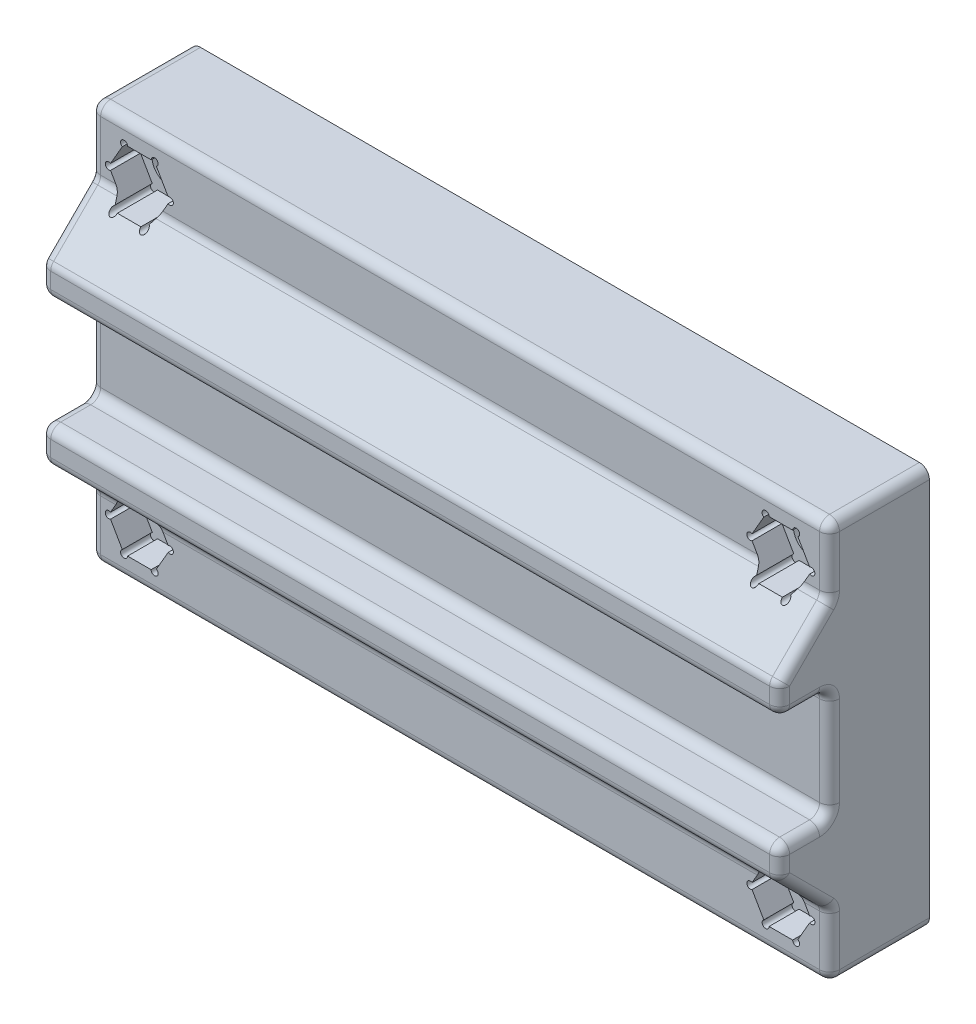
SolidWorks part; units mm, degrees
ref_plane "Front Plane" through (0, 0, 0) normal (0, 0, 1) x (1, 0, 0)
ref_plane "Top Plane" through (0, 0, 0) normal (0, 1, 0) x (1, 0, 0)
ref_plane "Right Plane" through (0, 0, 0) normal (1, 0, 0) x (0, 0, -1)
sketch "Sketch1" plane through (0, 0, 0) normal (0, 0, 1) x (1, 0, 0)
  line L7 (-37, -20) -> (37, -20)
  line L8 (-37, -20) -> (-37, 20)
  line L14 (-37, 20) -> (37, 20)
  line L15 (37, -20) -> (37, 20)
  line L18 (-37, -20) -> (37, 20) construction
  line L19 (-37, 20) -> (37, -20) construction
  point P0 (0, 0)
  dimension "D1" = 40
  dimension "D2" = 74
extrude "Boss-Extrude1" add sketch "Sketch1" along normal blind 10
sketch "Sketch2" plane through (-37, 0, 0) normal (-1, 0, 0) x (0, 0, 1)
  line L0 (10, 5.5) -> (15, 5.5)
  line L2 (15, 5.5) -> (15, 8.5)
  line L3 (15, 8.5) -> (10, 13.5)
  line L6 (10, 13.5) -> (10, 5.5)
  line L13 (0, 20) -> (0, -20)
  line L17 (0, -20) -> (10, -20)
  line L19 (10, -20) -> (10, 20)
  line L20 (10, 20) -> (0, 20)
  line L22 (0, 20) -> (0, -20) construction
  line L24 (0, -20) -> (10, -20) construction
  line L25 (10, -20) -> (10, 20) construction
  line L34 (10, 20) -> (0, 20) construction
  line L35 (0, 0) -> (10, 0) construction
  line L36 (10, -13.5) -> (10, -5.5)
  line L37 (15, -8.5) -> (10, -13.5)
  line L41 (15, -5.5) -> (15, -8.5)
  line L43 (10, -5.5) -> (15, -5.5)
  point P8 (10, 0)
  dimension "D2" = 3
  dimension "D3" = 5
  dimension "D4" = 5.5
  dimension "D5" = 45
  dimension "D1" = 0
extrude "Boss-Extrude2" add sketch "Sketch2" against normal up to surface (74 mm away) up to face at (37, 0, 5)
sketch "Sketch3" plane through (0, 0, 10) normal (0, 0, 1) x (1, 0, 0)
  line L0 (37, 20) -> (30.5, 13.5) construction
  line L1 (37, 13.5) -> (-37, 13.5) construction
  line L2 (37, 13.5) -> (37, 20) construction
  line L3 (33.75, 16.75) -> (30.5, 13.5) construction
  line L4 (8.25, 0) -> (-8.25, 0) construction
  line L5 (0, -8.25) -> (0, 8.25) construction
  circle A0 centre (32.125, 15.125) radius 1.75
  circle A1 centre (32.125, -15.125) radius 1.75
  circle A2 centre (-32.125, -15.125) radius 1.75
  circle A3 centre (-32.125, 15.125) radius 1.75
  point P22 (33.75, 16.75)
  dimension "D2" = 3.5
  dimension "D1" = 45
extrude "Cut-Extrude1" cut sketch "Sketch3" against normal through all both and the other way through all
sketch "Sketch4" plane through (0, 0, 10) normal (0, 0, 1) x (1, 0, 0)
  line L0 (30.595, 17.775) -> (30.42, 17.4719) construction
  line L7 (35.01, 15.4281) -> (33.83, 17.4719)
  line L8 (33.305, 17.775) -> (30.945, 17.775)
  line L9 (30.42, 17.4719) -> (29.24, 15.4281)
  line L10 (29.24, 14.8219) -> (30.42, 12.7781)
  line L11 (30.945, 12.475) -> (33.305, 12.475)
  line L12 (33.83, 12.7781) -> (35.01, 14.8219)
  line L13 (30.945, 17.775) -> (30.595, 17.775) construction
  line L14 (33.655, 17.775) -> (33.305, 17.775) construction
  line L15 (33.83, 17.4719) -> (33.655, 17.775) construction
  line L16 (35.185, 15.125) -> (35.01, 15.4281) construction
  line L17 (35.01, 14.8219) -> (35.185, 15.125) construction
  line L18 (33.655, 12.475) -> (33.83, 12.7781) construction
  line L19 (33.305, 12.475) -> (33.655, 12.475) construction
  line L20 (30.595, 12.475) -> (30.945, 12.475) construction
  line L21 (30.42, 12.7781) -> (30.595, 12.475) construction
  line L22 (29.065, 15.125) -> (29.24, 14.8219) construction
  line L23 (29.24, 15.4281) -> (29.065, 15.125) construction
  line L24 (-33.655, 17.775) -> (-33.83, 17.4719) construction
  line L25 (-29.24, 15.4281) -> (-30.42, 17.4719)
  line L26 (-30.945, 17.775) -> (-33.305, 17.775)
  line L27 (-33.83, 17.4719) -> (-35.01, 15.4281)
  line L28 (-35.01, 14.8219) -> (-33.83, 12.7781)
  line L29 (-33.305, 12.475) -> (-30.945, 12.475)
  line L30 (-30.42, 12.7781) -> (-29.24, 14.8219)
  line L31 (-33.305, 17.775) -> (-33.655, 17.775) construction
  line L32 (-30.595, 17.775) -> (-30.945, 17.775) construction
  line L33 (-30.42, 17.4719) -> (-30.595, 17.775) construction
  line L34 (-29.065, 15.125) -> (-29.24, 15.4281) construction
  line L35 (-29.24, 14.8219) -> (-29.065, 15.125) construction
  line L36 (-30.595, 12.475) -> (-30.42, 12.7781) construction
  line L37 (-30.945, 12.475) -> (-30.595, 12.475) construction
  line L38 (-33.83, 12.7781) -> (-33.655, 12.475) construction
  line L39 (-33.655, 12.475) -> (-33.305, 12.475) construction
  line L40 (-35.185, 15.125) -> (-35.01, 14.8219) construction
  line L41 (-35.01, 15.4281) -> (-35.185, 15.125) construction
  line L43 (-29.24, -14.8219) -> (-30.42, -12.7781)
  line L44 (-30.945, -12.475) -> (-33.305, -12.475)
  line L45 (-33.83, -12.7781) -> (-35.01, -14.8219)
  line L46 (-35.01, -15.4281) -> (-33.83, -17.4719)
  line L47 (-33.305, -17.775) -> (-30.945, -17.775)
  line L48 (-30.42, -17.4719) -> (-29.24, -15.4281)
  line L49 (-33.655, -12.475) -> (-33.83, -12.7781) construction
  line L50 (-30.595, -12.475) -> (-30.945, -12.475) construction
  line L51 (-30.42, -12.7781) -> (-30.595, -12.475) construction
  line L52 (-29.065, -15.125) -> (-29.24, -14.8219) construction
  line L53 (-29.24, -15.4281) -> (-29.065, -15.125) construction
  line L54 (-30.945, -17.775) -> (-30.595, -17.775) construction
  line L55 (-33.655, -17.775) -> (-33.305, -17.775) construction
  line L56 (-33.83, -17.4719) -> (-33.655, -17.775) construction
  line L57 (-35.01, -14.8219) -> (-35.185, -15.125) construction
  line L58 (-35.185, -15.125) -> (-35.01, -15.4281) construction
  line L59 (30.595, -12.475) -> (30.42, -12.7781) construction
  line L60 (35.01, -14.8219) -> (33.83, -12.7781)
  line L61 (33.305, -12.475) -> (30.945, -12.475)
  line L62 (30.42, -12.7781) -> (29.24, -14.8219)
  line L63 (29.24, -15.4281) -> (30.42, -17.4719)
  line L64 (30.945, -17.775) -> (33.305, -17.775)
  line L65 (33.83, -17.4719) -> (35.01, -15.4281)
  line L66 (30.945, -12.475) -> (30.595, -12.475) construction
  line L67 (33.655, -12.475) -> (33.305, -12.475) construction
  line L68 (33.83, -12.7781) -> (33.655, -12.475) construction
  line L69 (35.185, -15.125) -> (35.01, -14.8219) construction
  line L70 (35.01, -15.4281) -> (35.185, -15.125) construction
  line L71 (33.655, -17.775) -> (33.83, -17.4719) construction
  line L72 (33.305, -17.775) -> (33.655, -17.775) construction
  line L73 (30.595, -17.775) -> (30.945, -17.775) construction
  line L74 (30.42, -17.4719) -> (30.595, -17.775) construction
  line L75 (29.065, -15.125) -> (29.24, -15.4281) construction
  line L76 (29.24, -14.8219) -> (29.065, -15.125) construction
  line L77 (-33.305, -12.475) -> (-33.655, -12.475) construction
  line L78 (-30.595, -17.775) -> (-30.42, -17.4719) construction
  arc A0 (33.83, 17.4719) -> (33.305, 17.775) centre (33.655, 17.775) ccw
  arc A1 (32.7745, 13.5) -> (31.4755, 13.5) centre (32.125, 15.125) ccw construction
  arc A2 (32.7745, 13.5) -> (31.4755, 13.5) centre (32.125, 15.125) ccw construction
  circle A10 centre (32.125, 15.125) radius 2.65 construction
  arc A17 (30.945, 17.775) -> (30.42, 17.4719) centre (30.595, 17.775) ccw
  arc A18 (35.01, 14.8219) -> (35.01, 15.4281) centre (35.185, 15.125) ccw
  arc A19 (33.305, 12.475) -> (33.83, 12.7781) centre (33.655, 12.475) ccw
  arc A20 (30.42, 12.7781) -> (30.945, 12.475) centre (30.595, 12.475) ccw
  arc A21 (29.24, 15.4281) -> (29.24, 14.8219) centre (29.065, 15.125) ccw
  arc A22 (30.42, 17.4719) -> (30.945, 17.775) centre (30.595, 17.775) ccw construction
  arc A23 (33.305, 17.775) -> (33.83, 17.4719) centre (33.655, 17.775) ccw construction
  arc A24 (35.01, 15.4281) -> (35.01, 14.8219) centre (35.185, 15.125) ccw construction
  arc A25 (33.83, 12.7781) -> (33.305, 12.475) centre (33.655, 12.475) ccw construction
  arc A26 (30.945, 12.475) -> (30.42, 12.7781) centre (30.595, 12.475) ccw construction
  arc A27 (29.24, 14.8219) -> (29.24, 15.4281) centre (29.065, 15.125) ccw construction
  arc A28 (-31.4755, 13.5) -> (-32.7745, 13.5) centre (-32.125, 15.125) ccw construction
  arc A29 (-31.4755, 13.5) -> (-32.7745, 13.5) centre (-32.125, 15.125) ccw construction
  circle A30 centre (-32.125, 15.125) radius 2.65 construction
  arc A31 (-33.305, 17.775) -> (-33.83, 17.4719) centre (-33.655, 17.775) ccw
  arc A32 (-30.42, 17.4719) -> (-30.945, 17.775) centre (-30.595, 17.775) ccw
  arc A33 (-29.24, 14.8219) -> (-29.24, 15.4281) centre (-29.065, 15.125) ccw
  arc A34 (-30.945, 12.475) -> (-30.42, 12.7781) centre (-30.595, 12.475) ccw
  arc A35 (-33.83, 12.7781) -> (-33.305, 12.475) centre (-33.655, 12.475) ccw
  arc A36 (-35.01, 15.4281) -> (-35.01, 14.8219) centre (-35.185, 15.125) ccw
  arc A37 (-33.83, 17.4719) -> (-33.305, 17.775) centre (-33.655, 17.775) ccw construction
  arc A38 (-30.945, 17.775) -> (-30.42, 17.4719) centre (-30.595, 17.775) ccw construction
  arc A39 (-29.24, 15.4281) -> (-29.24, 14.8219) centre (-29.065, 15.125) ccw construction
  arc A40 (-30.42, 12.7781) -> (-30.945, 12.475) centre (-30.595, 12.475) ccw construction
  arc A41 (-33.305, 12.475) -> (-33.83, 12.7781) centre (-33.655, 12.475) ccw construction
  arc A42 (-35.01, 14.8219) -> (-35.01, 15.4281) centre (-35.185, 15.125) ccw construction
  arc A43 (-32.7745, -13.5) -> (-31.4755, -13.5) centre (-32.125, -15.125) ccw construction
  arc A44 (-32.7745, -13.5) -> (-31.4755, -13.5) centre (-32.125, -15.125) ccw construction
  circle A45 centre (-32.125, -15.125) radius 2.65 construction
  arc A46 (-33.305, -12.475) -> (-33.83, -12.7781) centre (-33.655, -12.475) ccw
  arc A47 (-30.42, -12.7781) -> (-30.945, -12.475) centre (-30.595, -12.475) ccw
  arc A48 (-29.24, -15.4281) -> (-29.24, -14.8219) centre (-29.065, -15.125) ccw
  arc A49 (-30.945, -17.775) -> (-30.42, -17.4719) centre (-30.595, -17.775) ccw
  arc A50 (-33.83, -17.4719) -> (-33.305, -17.775) centre (-33.655, -17.775) ccw
  arc A51 (-35.01, -14.8219) -> (-35.01, -15.4281) centre (-35.185, -15.125) ccw
  arc A52 (-33.83, -12.7781) -> (-33.305, -12.475) centre (-33.655, -12.475) ccw construction
  arc A53 (-30.945, -12.475) -> (-30.42, -12.7781) centre (-30.595, -12.475) ccw construction
  arc A54 (-29.24, -14.8219) -> (-29.24, -15.4281) centre (-29.065, -15.125) ccw construction
  arc A55 (-30.42, -17.4719) -> (-30.945, -17.775) centre (-30.595, -17.775) ccw construction
  arc A56 (-33.305, -17.775) -> (-33.83, -17.4719) centre (-33.655, -17.775) ccw construction
  arc A57 (-35.01, -15.4281) -> (-35.01, -14.8219) centre (-35.185, -15.125) ccw construction
  arc A58 (31.4755, -13.5) -> (32.7745, -13.5) centre (32.125, -15.125) ccw construction
  arc A59 (31.4755, -13.5) -> (32.7745, -13.5) centre (32.125, -15.125) ccw construction
  circle A60 centre (32.125, -15.125) radius 2.65 construction
  arc A61 (30.945, -12.475) -> (30.42, -12.7781) centre (30.595, -12.475) ccw
  arc A62 (33.83, -12.7781) -> (33.305, -12.475) centre (33.655, -12.475) ccw
  arc A63 (35.01, -15.4281) -> (35.01, -14.8219) centre (35.185, -15.125) ccw
  arc A64 (33.305, -17.775) -> (33.83, -17.4719) centre (33.655, -17.775) ccw
  arc A65 (30.42, -17.4719) -> (30.945, -17.775) centre (30.595, -17.775) ccw
  arc A66 (29.24, -14.8219) -> (29.24, -15.4281) centre (29.065, -15.125) ccw
  arc A67 (30.42, -12.7781) -> (30.945, -12.475) centre (30.595, -12.475) ccw construction
  arc A68 (33.305, -12.475) -> (33.83, -12.7781) centre (33.655, -12.475) ccw construction
  arc A69 (35.01, -14.8219) -> (35.01, -15.4281) centre (35.185, -15.125) ccw construction
  arc A70 (33.83, -17.4719) -> (33.305, -17.775) centre (33.655, -17.775) ccw construction
  arc A71 (30.945, -17.775) -> (30.42, -17.4719) centre (30.595, -17.775) ccw construction
  arc A72 (29.24, -15.4281) -> (29.24, -14.8219) centre (29.065, -15.125) ccw construction
  point P23 (32.125, 15.125)
  point P51 (-32.125, 15.125)
  point P77 (-32.125, -15.125)
  point P104 (32.125, -15.125)
  dimension "D1" = 5.3
  dimension "0.7" = 0.7
  dimension "D4" = 5.3
  dimension "D5" = 0.7
  dimension "D7" = 5.3
  dimension "D8" = 0.7
  dimension "D9" = 5.3
  dimension "D10" = 0.7
  dimension "D3" = 6
  dimension "D6" = 6
extrude "Cut-Extrude2" cut sketch "Sketch4" against normal blind 3 and the other way through all
fillet "Fillet1" radius 1 36 edges at (-37, 5.5, 12.5) (-37, -5.5, 12.5) (37, 5.5, 12.5) (37, -5.5, 12.5) (37, -16.75, 10) (-37, -11, 12.5) (-37, 16.75, 10) (37, 16.75, 10) (-37, -7, 15) (0, -5.5, 15) (37, -7, 15) (0, -8.5, 15) (-37, 0, 10) (0, 5.5, 10) (37, 0, 10) (0, -5.5, 10) (0, 5.5, 15) (-37, 7, 15) (0, 8.5, 15) (37, 7, 15) (37, 20, 5) (-37, 20, 5) (-37, -20, 5) (37, -20, 5) (37, -11, 12.5) (35.6234, -13.5, 10) (0, -20, 10) (0, -13.5, 10) (-37, -16.75, 10) (-35.6234, -13.5, 10) (-35.6234, 13.5, 10) (-37, 11, 12.5) (37, 11, 12.5) (35.6234, 13.5, 10) (0, 13.5, 10) (0, 20, 10)
equation "\"m3_nut\"= 5.3"
equation "\"m3_hole\"= 3.5"
equation "\"m3_washer\"= 7.3"
equation "\"guide_width\"= 10.0"
equation "\"D1@Sketch1\"=\"guide_width\"+30"
equation "\"guide_diameter\"= 64.0"
equation "\"guide_tab_length\" = 10.0"
equation "\"guide_tab_width\" = 9.0"
equation "\"D2@Sketch1\"=\"guide_diameter\"+\"guide_tab_length\""
equation "\"D4@Sketch2\"=\"guide_width\"/2 +0.5"
equation "\"D2@Sketch3\"=\"m3_hole\""
equation "\"D1@Sketch4\"=\"m3_nut\""
equation "\"D4@Sketch4\"=\"m3_nut\""
equation "\"D7@Sketch4\"=\"m3_nut\""
equation "\"D9@Sketch4\"=\"m3_nut\""
